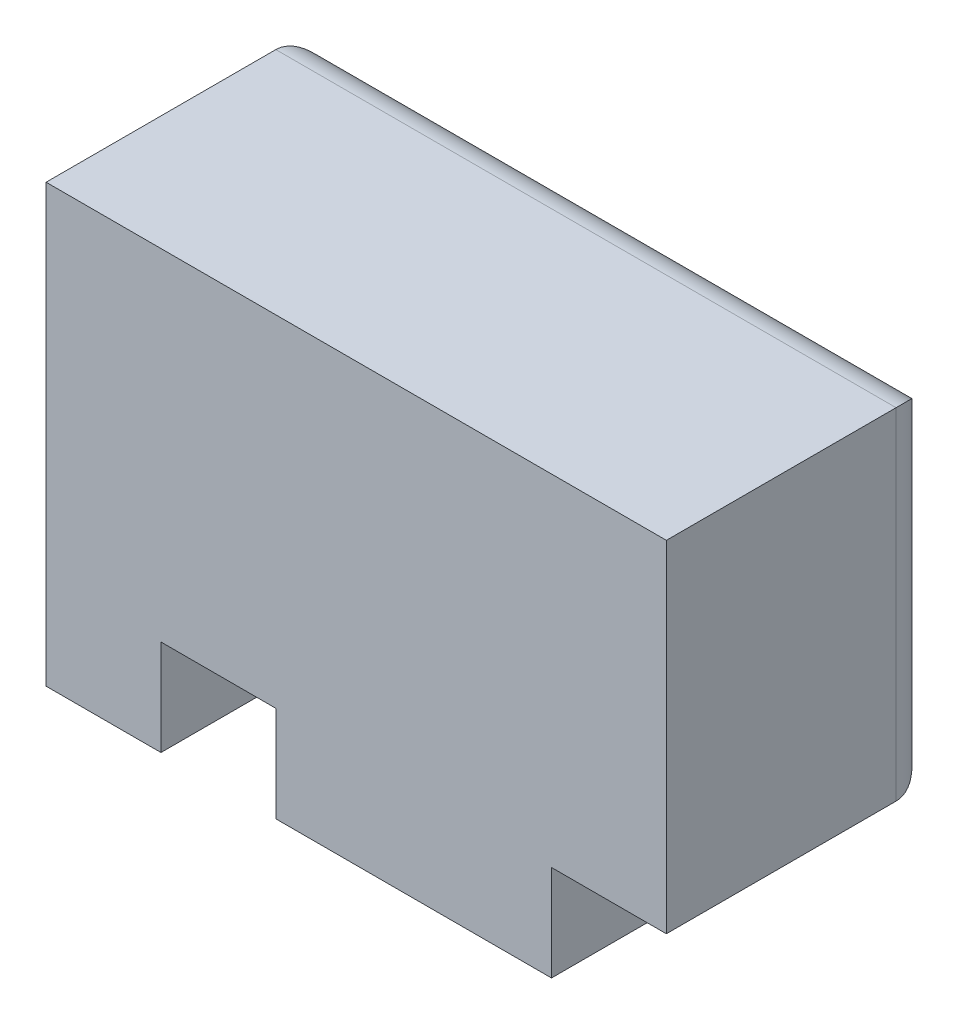
SolidWorks part; units mm, degrees
ref_plane "Přední rovina" through (0, 0, 0) normal (0, 0, 1) x (1, 0, 0)
ref_plane "Horní rovina" through (0, 0, 0) normal (0, 1, 0) x (1, 0, 0)
ref_plane "Pravá rovina" through (0, 0, 0) normal (1, 0, 0) x (0, 0, -1)
sketch "Skica1" plane through (0, 0, 0) normal (0, 0, 1) x (1, 0, 0)
  line L1 (0, 0) -> (16.2, 0)
  line L2 (0, 0) -> (0, 11.4)
  line L3 (0, 11.4) -> (16.2, 11.4)
  line L4 (16.2, 0) -> (16.2, 11.4)
  dimension "D1" = 16.2
  dimension "D2" = 11.4
extrude "Přidat vysunutím1" add sketch "Skica1" along normal blind 7
sketch "Skica2" plane through (0, 0, 7) normal (0, 0, 1) x (1, 0, 0)
  line L0 (0, 0) -> (16.2, 0) construction
  line L1 (3, 0) -> (6, 0)
  line L2 (3, 0) -> (3, 2.5)
  line L3 (3, 2.5) -> (6, 2.5)
  line L4 (6, 0) -> (6, 2.5)
  line L6 (13.2, 0) -> (16.2, 0)
  line L7 (13.2, 0) -> (13.2, 2.5)
  line L8 (13.2, 2.5) -> (16.2, 2.5)
  line L9 (16.2, 0) -> (16.2, 2.5)
  line L10 (6, 2.5) -> (13.2, 2.5)
  line L11 (16.2, 0) -> (16.2, 11.4) construction
  line L12 (0, 11.4) -> (0, 0) construction
  line M10 (0, 0) -> (16.2, 0)
  dimension "D1" = 3
  dimension "D2" = 3
  dimension "D3" = 3
  dimension "D5" = 2.5
extrude "Odebrat vysunutím1" cut sketch "Skica2" against normal through all contours L4 L3 L2 M10 | L9 L8 L7 M10
fillet "Zaoblit5" radius 1 10 edges at (6, 1.25, 0) (9.6, 0, 0) (13.2, 1.25, 0) (14.7, 2.5, 0) (16.2, 6.95, 0) (8.1, 11.4, 0) (0, 5.7, 0) (1.5, 0, 0) (3, 1.25, 0) (4.5, 2.5, 0)
